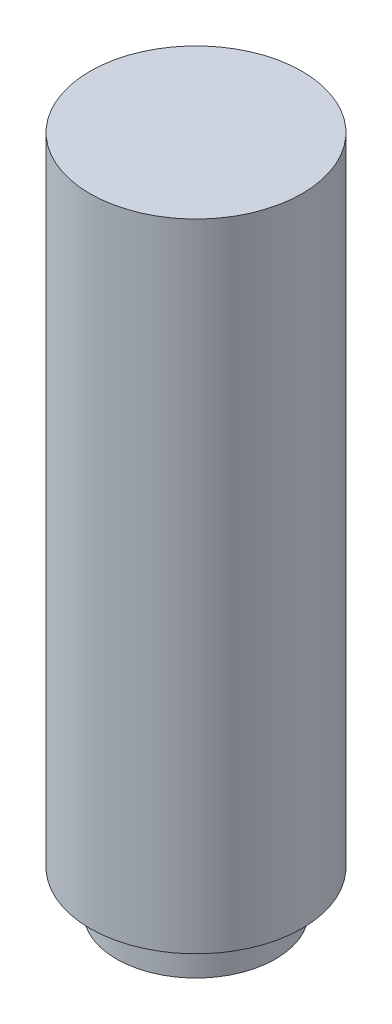
SolidWorks part; units mm, degrees
ref_plane "Front Plane" through (0, 0, 0) normal (0, 0, 1) x (1, 0, 0)
ref_plane "Top Plane" through (0, 0, 0) normal (0, 1, 0) x (1, 0, 0)
ref_plane "Right Plane" through (0, 0, 0) normal (1, 0, 0) x (0, 0, -1)
sketch "Sketch1" plane through (0, 0, 0) normal (0, 1, 0) x (1, 0, 0)
  circle A0 centre (0, 0) radius 40
  dimension "D1" = 80
extrude "Boss-Extrude1" add sketch "Sketch1" along normal blind 240
sketch "Sketch2" plane through (0, 0, 0) normal (0, -1, 0) x (1, 0, 0)
  circle A0 centre (0, 0) radius 30
  dimension "60" = 60
extrude "Boss-Extrude2" add sketch "Sketch2" along normal blind 15
sketch "Sketch3" plane through (0, -15, 0) normal (0, -1, 0) x (1, 0, 0)
  circle A0 centre (0, 0) radius 12.5
  dimension "D1" = 25
extrude "Cut-Extrude2" cut sketch "Sketch3" against normal blind 10 contours A0
